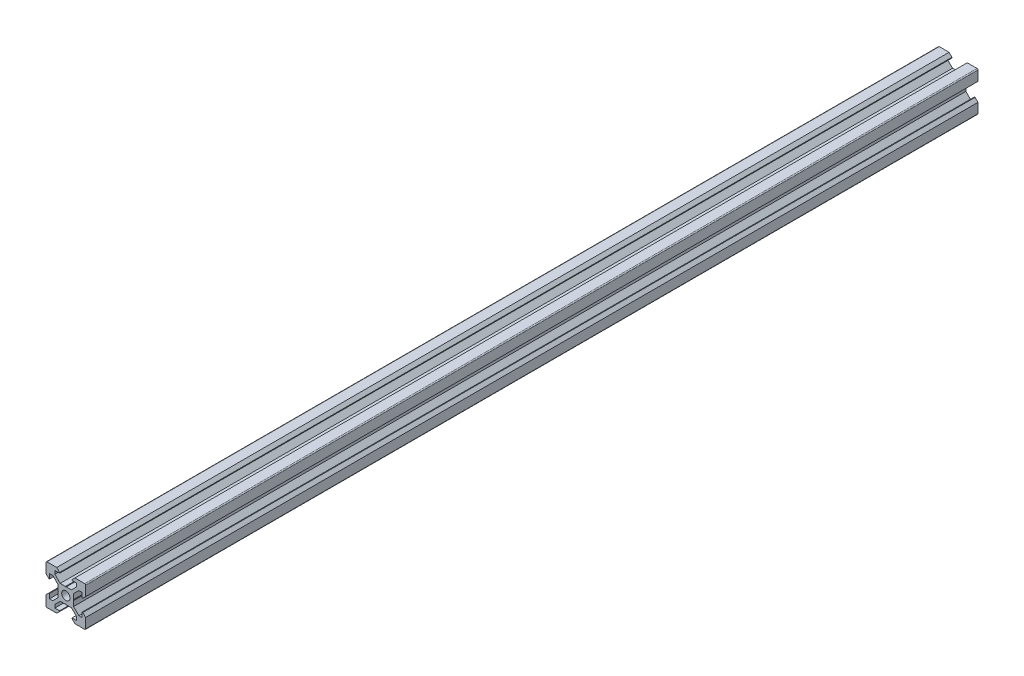
SolidWorks part; units mm, degrees
material "6061-T6 (SS)"
ref_plane "Front Plane" through (0, 0, 0) normal (0, 0, 1) x (1, 0, 0)
ref_plane "Top Plane" through (0, 0, 0) normal (0, 1, 0) x (1, 0, 0)
ref_plane "Right Plane" through (0, 0, 0) normal (1, 0, 0) x (0, 0, -1)
sketch "Sketch1" plane through (0, 0, 0) normal (0, 0, 1) x (1, 0, 0)
  line L1 (9.5, -10) -> (-9.5, -10)
  line L2 (10, -9.5) -> (10, 9.5)
  line L3 (9.5, 10) -> (-9.5, 10)
  line L4 (-10, -9.5) -> (-10, 9.5)
  line L5 (10, -10) -> (-10, 10) construction
  line L6 (10, 10) -> (-10, -10) construction
  circle A0 centre (0, 0) radius 2.1
  arc A1 (-9.5, 10) -> (-10, 9.5) centre (-9.5, 9.5) ccw
  arc A2 (10, 9.5) -> (9.5, 10) centre (9.5, 9.5) ccw
  arc A3 (9.5, -10) -> (10, -9.5) centre (9.5, -9.5) ccw
  arc A4 (-9.5, -10) -> (-10, -9.5) centre (-9.5, -9.5) cw
  point P0 (0, 0)
  line B0 (0, 0) -> (0, 10) construction
  line B1 (0, 3.69) -> (-0.21, 3.9)
  line B2 (-0.21, 3.9) -> (-2.8393, 3.9)
  line B3 (-2.8393, 3.9) -> (-5.5, 6.5607)
  line B4 (-5.5, 6.5607) -> (-5.5, 8.2)
  line B5 (-5.5, 8.2) -> (-3.125, 8.2)
  line B6 (-3.125, 8.2) -> (-3.125, 8.545)
  line B7 (-3.125, 8.545) -> (-4.58, 10)
  line B8 (-4.58, 10) -> (4.58, 10)
  line B9 (0, 0) -> (-5.9132, 5.9132) construction
  line B10 (3.125, 8.545) -> (4.58, 10)
  line B11 (3.125, 8.2) -> (3.125, 8.545)
  line B12 (5.5, 8.2) -> (3.125, 8.2)
  line B13 (5.5, 6.5607) -> (5.5, 8.2)
  line B14 (2.8393, 3.9) -> (5.5, 6.5607)
  line B15 (0.21, 3.9) -> (2.8393, 3.9)
  line B16 (0, 3.69) -> (0.21, 3.9)
  line B17 (0, 0) -> (-10, 0) construction
  line B18 (-3.69, 0) -> (-3.9, -0.21)
  line B19 (-3.9, -0.21) -> (-3.9, -2.8393)
  line B20 (-3.9, -2.8393) -> (-6.5607, -5.5)
  line B21 (-6.5607, -5.5) -> (-8.2, -5.5)
  line B22 (-8.2, -5.5) -> (-8.2, -3.125)
  line B23 (-8.2, -3.125) -> (-8.545, -3.125)
  line B24 (-8.545, -3.125) -> (-10, -4.58)
  line B25 (-10, -4.58) -> (-10, 4.58)
  line B26 (0, 0) -> (-5.9132, -5.9132) construction
  line B27 (-8.545, 3.125) -> (-10, 4.58)
  line B28 (-8.2, 3.125) -> (-8.545, 3.125)
  line B29 (-8.2, 5.5) -> (-8.2, 3.125)
  line B30 (-6.5607, 5.5) -> (-8.2, 5.5)
  line B31 (-3.9, 2.8393) -> (-6.5607, 5.5)
  line B32 (-3.9, 0.21) -> (-3.9, 2.8393)
  line B33 (-3.69, 0) -> (-3.9, 0.21)
  line B34 (0, 0) -> (0, -10) construction
  line B35 (0, -3.69) -> (0.21, -3.9)
  line B36 (0.21, -3.9) -> (2.8393, -3.9)
  line B37 (2.8393, -3.9) -> (5.5, -6.5607)
  line B38 (5.5, -6.5607) -> (5.5, -8.2)
  line B39 (5.5, -8.2) -> (3.125, -8.2)
  line B40 (3.125, -8.2) -> (3.125, -8.545)
  line B41 (3.125, -8.545) -> (4.58, -10)
  line B42 (4.58, -10) -> (-4.58, -10)
  line B43 (0, 0) -> (5.9132, -5.9132) construction
  line B44 (-3.125, -8.545) -> (-4.58, -10)
  line B45 (-3.125, -8.2) -> (-3.125, -8.545)
  line B46 (-5.5, -8.2) -> (-3.125, -8.2)
  line B47 (-5.5, -6.5607) -> (-5.5, -8.2)
  line B48 (-2.8393, -3.9) -> (-5.5, -6.5607)
  line B49 (-0.21, -3.9) -> (-2.8393, -3.9)
  line B50 (0, -3.69) -> (-0.21, -3.9)
  line B51 (0, 0) -> (10, 0) construction
  line B52 (3.69, 0) -> (3.9, 0.21)
  line B53 (3.9, 0.21) -> (3.9, 2.8393)
  line B54 (3.9, 2.8393) -> (6.5607, 5.5)
  line B55 (6.5607, 5.5) -> (8.2, 5.5)
  line B56 (8.2, 5.5) -> (8.2, 3.125)
  line B57 (8.2, 3.125) -> (8.545, 3.125)
  line B58 (8.545, 3.125) -> (10, 4.58)
  line B59 (10, 4.58) -> (10, -4.58)
  line B60 (0, 0) -> (5.9132, 5.9132) construction
  line B61 (8.545, -3.125) -> (10, -4.58)
  line B62 (8.2, -3.125) -> (8.545, -3.125)
  line B63 (8.2, -5.5) -> (8.2, -3.125)
  line B64 (6.5607, -5.5) -> (8.2, -5.5)
  line B65 (3.9, -2.8393) -> (6.5607, -5.5)
  line B66 (3.9, -0.21) -> (3.9, -2.8393)
  line B67 (3.69, 0) -> (3.9, -0.21)
  dimension "D1" = 4.2
  dimension "D3" = 0.5
  dimension "D2" = 20
sketch_block_instance "V Slot 1-4"
sketch_block "V Slot 1" parameters "D1"=10, "D2"=11, "D3"=4.3, "D4"=1.8, "D5"=0.21, "D6"=45, "D7"=9.16, "D8"=1.5, "D9"=6.25
sketch_block_instance "V Slot 1-5"
sketch_block_instance "V Slot 1-6"
sketch_block_instance "V Slot 1-7"
extrude "Boss-Extrude1" add sketch "Sketch1" along normal blind 450 contours B67 B52 B53 B54 B55 B56 B57 B58 L2 A2 L3 B10 B11 B12 B13 B14 B15 B16 B1 B2 B3 B4 B5 B6 B7 A1 L4 B27 B28 B29 B30 B31 B32 B33 B18 B19 B20 B21 B22 B23 B24 A4 L1 B44 B45 B46 B47 B48 B49
